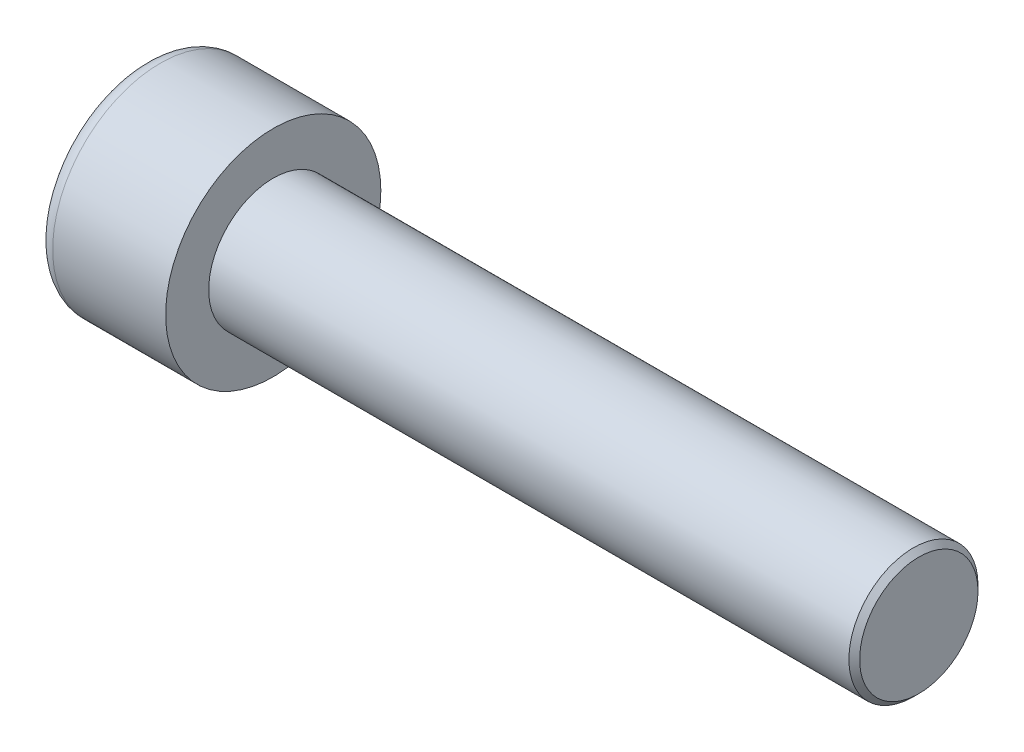
SolidWorks part; units mm, degrees
ref_plane "Front" through (0, 0, 0) normal (0, 0, 1) x (1, 0, 0)
ref_plane "Top" through (0, 0, 0) normal (0, 1, 0) x (1, 0, 0)
ref_plane "Right" through (0, 0, 0) normal (1, 0, 0) x (0, 0, -1)
sketch "Sketch1" plane through (0, 0, 0) normal (1, 0, 0) x (0, 0, -1)
  circle A0 centre (0, 0) radius 5
  dimension "dk" = 10
extrude "BaseHead" add sketch "Sketch1" along normal blind 6
sketch "Sketch2" plane through (6, 0, 0) normal (1, 0, 0) x (0, 0, -1)
  circle A0 centre (0, 0) radius 3
  dimension "d" = 6
extrude "BaseBody" add sketch "Sketch2" along normal blind 30
cosmetic thread "ThreadCosmetic1" parameters "b"=30, "D2"=4.917
sketch "Sketch3" plane through (0, 0, 0) normal (1, 0, 0) x (0, 0, -1)
  line L1 (2.8868, 0) -> (1.4434, 2.5)
  line L2 (1.4434, 2.5) -> (-1.4434, 2.5)
  line L3 (-1.4434, 2.5) -> (-2.8868, 0)
  line L4 (-2.8868, 0) -> (-1.4434, -2.5)
  line L5 (-1.4434, -2.5) -> (1.4434, -2.5)
  line L6 (1.4434, -2.5) -> (2.8868, 0)
  circle A0 centre (0, 0) radius 2.5 construction
  dimension "s" = 5
  dimension "e" = 5.7735
extrude "HexagonSocket" cut sketch "Sketch3" along normal blind 3
sketch "Sketch4" plane through (-4.1961, 0.75, 0) normal (0, 0, 1) x (-1, 0, 0)
  line L0 (-7.1961, 3.25) -> (-8.6395, 0.75)
  line L2 (-8.6395, 0.75) -> (-7.1961, 0.75)
  line L3 (-7.1961, 0.75) -> (-7.1961, 3.25)
  line L4 (-5.0351, 0.75) -> (0.839, 0.75) construction
  line L5 (-40.1961, 0.75) -> (-10.1961, 0.75) construction
  line L6 (-10.1961, 0.75) -> (-4.1961, 0.75) construction
  dimension "m" = 60
revolve "Cut-Revolve1" cut sketch "Sketch4" angle 360 about L4
fillet "HeadFillet" [suppressed] radius 0.25
fillet "TopFillet" radius 0.75 1 edges at (0, 0, -5)
chamfer "Chamfer1" distance 0.25 angle 45 1 edges at (36, 0, -3)
sketch "Sketch5" plane through (0, 0, 0) normal (0, 0, 1) x (1, 0, 0)
  line L0 (35.75, 2.531) -> (36.0207, 3)
  line L1 (36.0207, 3) -> (36.0207, 3.5415)
  line L2 (36.0207, 3.5415) -> (35.4793, 3.5415)
  line L3 (35.4793, 3.5415) -> (35.4793, 3)
  line L4 (35.4793, 3) -> (35.75, 2.531)
  line L5 (0, 0) -> (7.8886, 0) construction
  line L6 (35.75, -3) -> (35.75, 3) construction
  dimension "D1" = 6
  dimension "D2" = 0.5415
revolve "Cut-Revolve10" [suppressed] cut sketch "Sketch5" angle 360 about L5
pattern_linear "LPattern10" [suppressed] count 46 spacing 0.6498 along (1, 0, 0)
equation "\"r1@TopFillet\" = \"d@Sketch2\" / 8"
equation "\"D1@Chamfer1\" = \"r@HeadFillet\""
equation "\"D1@Sketch5\" = \"d@Sketch2\""
equation "\"D2@Sketch5\" =  ( \"d@Sketch2\" - \"D2@ThreadCosmetic1\" )  / 2"
equation "\"D3@LPattern10\" = \"D2@Sketch5\" * 1.2"
equation "\"D1@LPattern10\" = \"b@ThreadCosmetic1\" / \"D3@LPattern10\""
